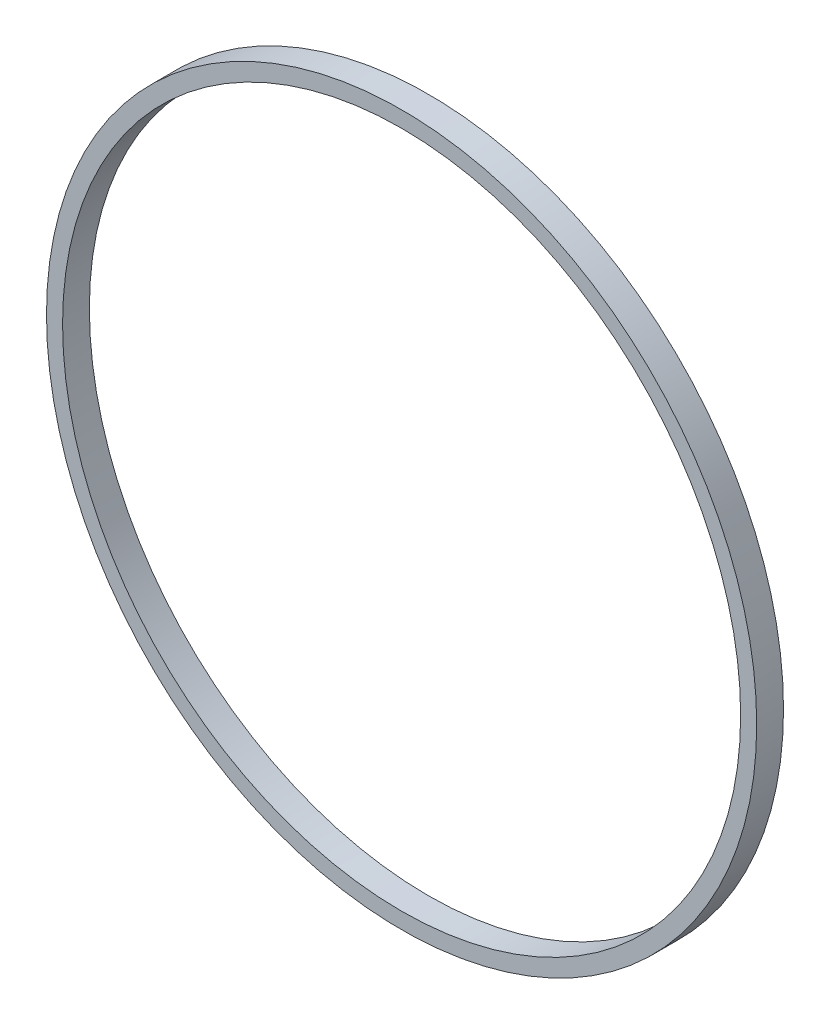
SolidWorks part; units mm, degrees
ref_plane "Alzado" through (0, 0, 0) normal (0, 0, 1) x (1, 0, 0)
ref_plane "Planta" through (0, 0, 0) normal (0, 1, 0) x (1, 0, 0)
ref_plane "Vista lateral" through (0, 0, 0) normal (1, 0, 0) x (0, 0, -1)
sketch "Croquis1" plane through (0, 0, 0) normal (0, 0, 1) x (1, 0, 0)
  circle A0 centre (0, 0) radius 66.25
  circle A1 centre (0, 0) radius 63.25
  dimension "D1" = 126.5
  dimension "D2" = 132.5
extrude "Saliente-Extruir1" add sketch "Croquis1" along normal blind 5
